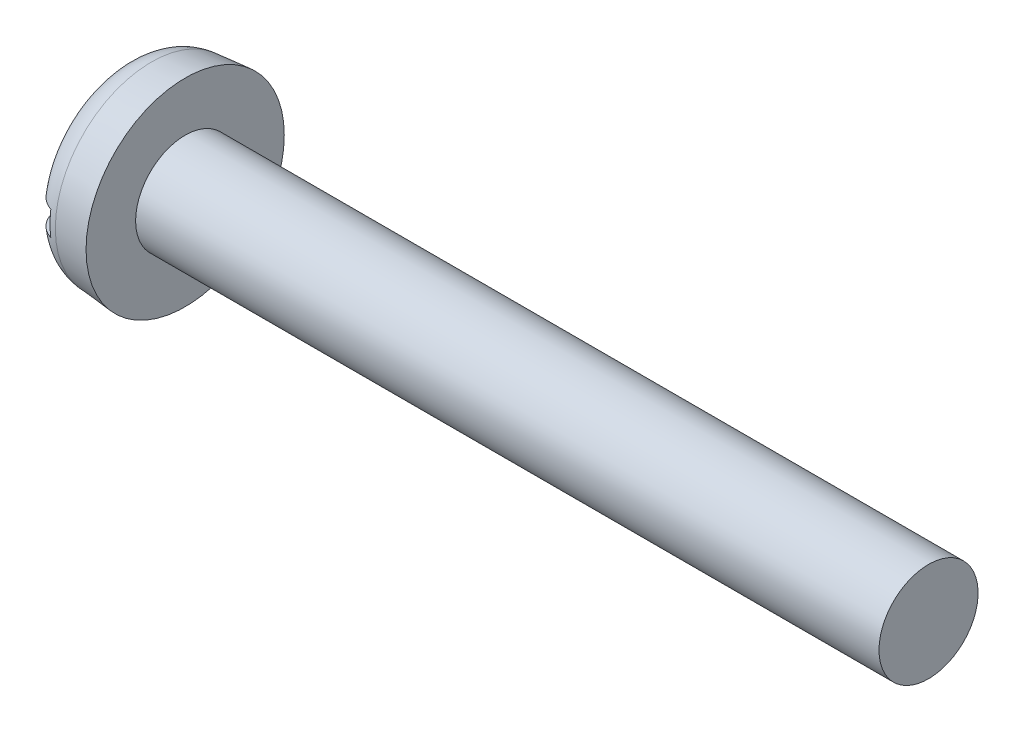
SolidWorks part; units mm, degrees
ref_plane "Plane1" through (0, 0, 0) normal (0, 0, 1) x (1, 0, 0)
ref_plane "Plane2" through (0, 0, 0) normal (0, 1, 0) x (1, 0, 0)
ref_plane "Plane3" through (0, 0, 0) normal (1, 0, 0) x (0, 0, -1)
sketch "BodySke" plane through (0, 0, 0) normal (0, 0, 1) x (1, 0, 0)
  line L0 (1, 0.8) -> (1, 1.6)
  line L1 (0, 0) -> (0, 1.5125)
  line L2 (-25.4, 0) -> (127, 0) construction
  line L3 (13, 0) -> (0, 0)
  line L4 (1, 0.8) -> (13, 0.8)
  line L5 (13, 0.8) -> (13, 0)
  line L6 (0, 1.5125) -> (1, 1.6)
  line L9 (1.35, 2.3875) -> (1.35, -7.1375) construction
  line L10 (1, 6.35) -> (1, -3.175) construction
  dimension "Length" = 12
  dimension "Head_ht" = 1
  dimension "Advance" = 0.35
  dimension "Thread_nom" = 12
  dimension "Head_dia" = 3.2
  dimension "Head_side_angle" = 5
  dimension "Diameter" = 1.6
revolve "Base-Revolve" add sketch "BodySke"
cosmetic thread "ThreadCosmetic" [suppressed]
fillet "Fillet1" [suppressed] radius 0.1
fillet "Fillet2" radius 0.5 1 edges at (0, 0, 1.5125)
sketch "Sketch2" plane through (0, 0, 0) normal (1, 0, 0) x (0, 0, -1)
  line L0 (1.6, -0.2) -> (-1.6, -0.2)
  line L1 (1.6, -0.2) -> (1.6, 0.2)
  line L2 (-1.6, 0.2) -> (1.6, 0.2)
  line L3 (-1.6, 0.2) -> (-1.6, -0.2)
  dimension "D1" = 3.2
  dimension "Slot_width" = 0.4
  dimension "D2" = 1.6
  dimension "D3" = 0.2
extrude "Slot" cut sketch "Sketch2" along normal blind 0.35
sketch "ThdSchSke" plane through (0, 0, 0) normal (0, 0, 1) x (1, 0, 0)
  line L0 (1.7, -0.601) -> (1.5607, -0.8)
  line L1 (1.7, -0.601) -> (1.8393, -0.8)
  line L2 (1.8393, -0.8) -> (1.8393, -1)
  line L3 (-3.175, 0) -> (5.1513, 0) construction
  line L5 (1.8393, -1) -> (1.5607, -1)
  line L6 (1.5607, -1) -> (1.5607, -0.8)
  dimension "Diameter" = 1.6
  dimension "SideAngle" = 55
  dimension "VeeAngle" = 70
  dimension "Thread_minor" = 1.202
  dimension "Overcut" = 2
  dimension "Start" = 1.7
revolve "ThreadSchematic" [suppressed] cut sketch "ThdSchSke" angle 360 about L3
pattern_linear "ThdSchPat" [suppressed]
equation "\"D1@Sketch2\" = \"Head_dia@BodySke\""
equation "\"D2@Sketch2\" = \"D1@Sketch2\" / 2"
equation "\"D3@Sketch2\" = \"Slot_width@Sketch2\" / 2"
equation "\"Thread_length@ThreadCosmetic\" = ((sgn( (\"Length@BodySke\" - \"Advance@BodySke\" * 2.0 ) - \"Thread_nom@BodySke\" )-1)*( (\"Length@BodySke\" - \"Advance@BodySke\"  * 2.0) - \"Thread_nom@BodySke\" ))/-2+ \"Thread_nom@BodySke\""
equation "\"Thread_minor@ThdSchSke\" = \"Thread_minor@ThreadCosmetic\""
equation "\"Diameter@ThdSchSke\" = \"Diameter@BodySke\""
equation "\"Overcut@ThdSchSke\" = \"Diameter@BodySke\" * 1.25"
equation "\"Start@ThdSchSke\" = \"Head_ht@BodySke\" + \"Length@BodySke\" - \"Thread_length@ThreadCosmetic\"  '---Non-countersunk---"
equation "\"Num_threads@ThdSchPat\" = int( \"Thread_length@ThreadCosmetic\" / \"Advance@BodySke\" + 0.999 )  + 1"
equation "\"Advance@ThdSchPat\" = \"Thread_length@ThreadCosmetic\" /  (\"Num_threads@ThdSchPat\" - 1) 'relax it"
